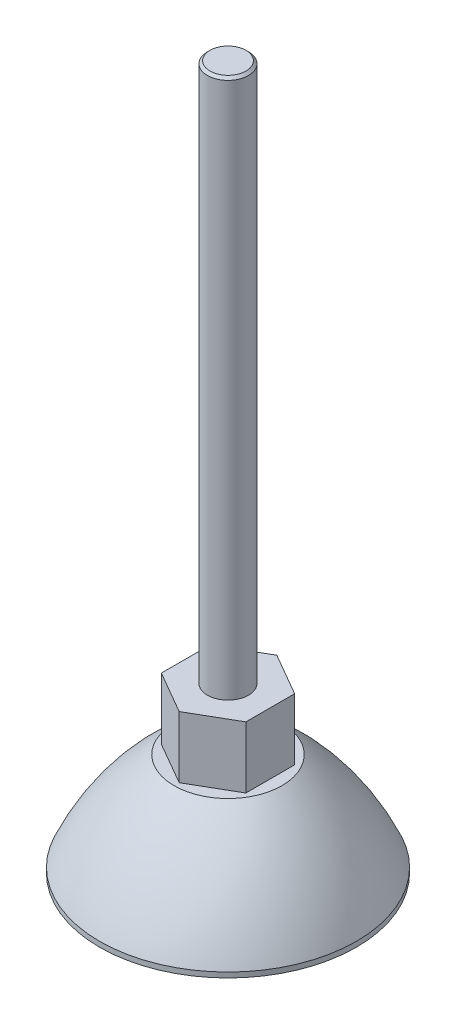
SolidWorks part; units mm, degrees
ref_plane "Спереди" through (0, 0, 0) normal (0, 0, 1) x (1, 0, 0)
ref_plane "Сверху" through (0, 0, 0) normal (0, 1, 0) x (1, 0, 0)
ref_plane "Справа" through (0, 0, 0) normal (1, 0, 0) x (0, 0, -1)
sketch "Эскиз1" plane through (0, 0, 0) normal (0, 0, 1) x (1, 0, 0)
  line L1 (0, 137) -> (-4, 137)
  line L2 (-4, 137) -> (-4, 32)
  line L3 (-4, 32) -> (-9.5, 32)
  line L4 (-9.5, 32) -> (-9.5, 20)
  line L7 (-9.5, 20) -> (-10.5, 20)
  line L8 (-10.5, 20) -> (-25, 1) construction
  line L9 (-25, 1) -> (-25, 0)
  line L10 (-25, 0) -> (0, 0)
  line L11 (0, 0) -> (0, 137) construction
  line L14 (0, 137) -> (0, 0)
  arc A0 (-25, 1) -> (-10.5, 20) centre (20.8456, -18.9545) cw
  point P0 (-10.3885, 20)
  point P7 (0.3428, 0)
  point P8 (-9.5, 20)
  point P16 (0, 0)
  point P17 (0, 0)
  point P18 (-14.6631, 7)
  point P19 (-10, 19.838)
  dimension "D13" = 50
  dimension "D2" = 1
  dimension "D3" = 20
  dimension "D4" = 25
  dimension "D5" = 1
  dimension "D6" = 9.5
  dimension "D7" = 12
  dimension "D9" = 4
  dimension "D10" = 105
revolve "Повернуть1" add sketch "Эскиз1" angle 360 about L11
cosmetic thread "Условное изображение резьбы1" parameters "D2"=6.619
chamfer "Фаска1" distance 0.5 angle 45 1 edges at (4, 137, 0)
sketch "Эскиз3" plane through (0, 32, 0) normal (0, 1, 0) x (1, 0, 0)
  line L1 (0, 9.5) -> (-8.2272, 4.75)
  line L2 (-8.2272, 4.75) -> (-8.2272, -4.75)
  line L3 (-8.2272, -4.75) -> (0, -9.5)
  line L4 (0, -9.5) -> (8.2272, -4.75)
  line L5 (8.2272, -4.75) -> (8.2272, 4.75)
  line L6 (8.2272, 4.75) -> (0, 9.5)
  circle A0 centre (0, 0) radius 8.2272 construction
  circle A1 centre (0, 0) radius 9.5 construction
  circle A2 centre (0, 0) radius 25
extrude "Вырез-Вытянуть1" cut sketch "Эскиз3" against normal up to surface (12 mm away) up to face at (10.5, 20, 0)
